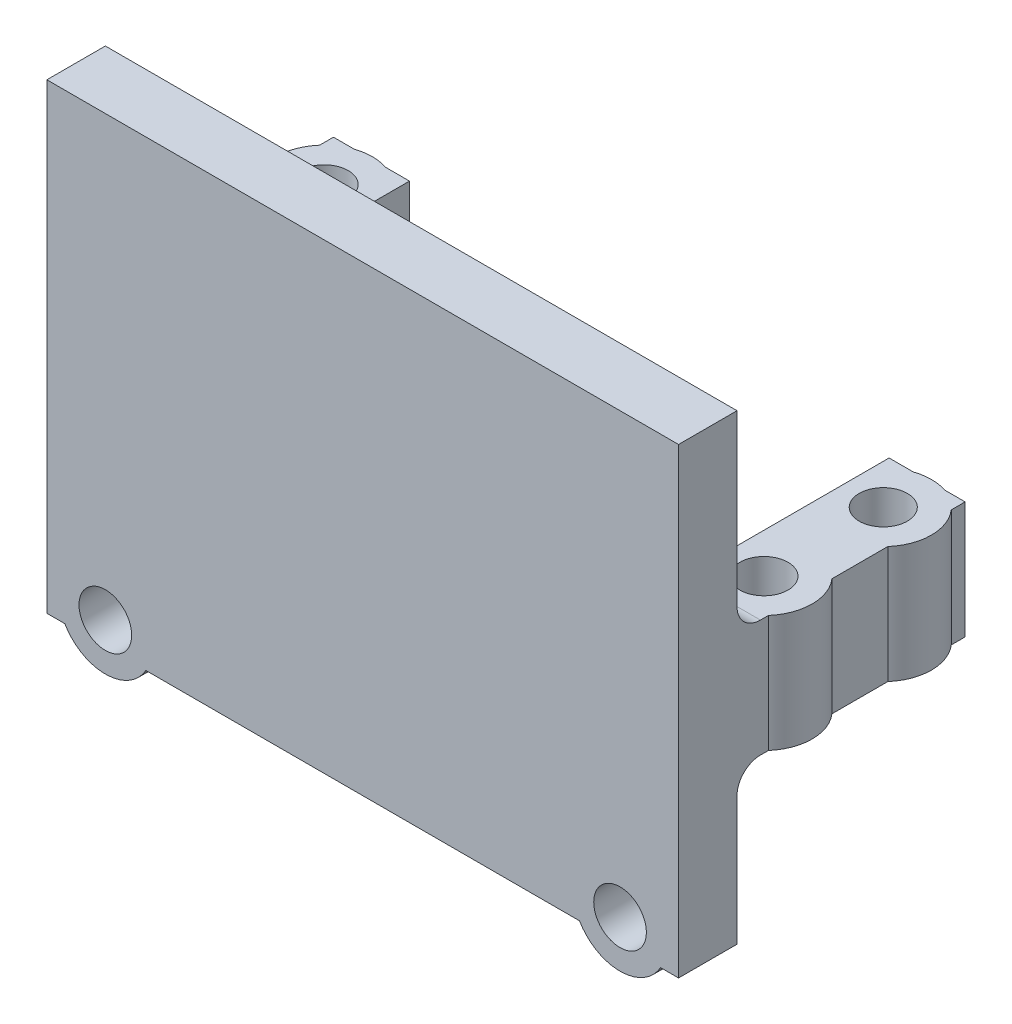
SolidWorks part; units mm, degrees
ref_plane "Front Plane" through (0, 0, 0) normal (0, 0, 1) x (1, 0, 0)
ref_plane "Top Plane" through (0, 0, 0) normal (0, 1, 0) x (1, 0, 0)
ref_plane "Right Plane" through (0, 0, 0) normal (1, 0, 0) x (0, 0, -1)
sketch "Sketch1" plane through (0, 0, 0) normal (0, 0, 1) x (1, 0, 0)
  line L1 (-27, 13.25) -> (27, 13.25)
  line L2 (-27, 13.25) -> (-27, -13.25)
  line L3 (-27, -13.25) -> (27, -13.25)
  line L4 (27, 13.25) -> (27, -13.25)
  dimension "D1" = 54
  dimension "D2" = 27
  dimension "D3" = 26.5
  dimension "D4" = 13.25
extrude "Boss-Extrude1" add sketch "Sketch1" along normal blind 5 contours L1 L4 L3 L2
sketch "Sketch2" plane through (0, 0, 0) normal (0, 0, -1) x (-1, 0, 0)
  line L0 (0, 0) -> (0, -16.6627) construction
  line L1 (-27, -13.25) -> (-20.5, -13.25)
  line L2 (-27, -13.25) -> (-27, -3.25)
  line L3 (-27, -3.25) -> (-20.5, -3.25)
  line L4 (-20.5, -13.25) -> (-20.5, -3.25)
  line L5 (20.5, -13.25) -> (20.5, -3.25)
  line L6 (27, -3.25) -> (20.5, -3.25)
  line L7 (27, -13.25) -> (27, -3.25)
  line L8 (27, -13.25) -> (20.5, -13.25)
  dimension "D1" = 6.5
  dimension "D2" = 10
extrude "Boss-Extrude2" add sketch "Sketch2" along normal blind 19.5
sketch "Sketch3" plane through (0, -13.25, 0) normal (0, -1, 0) x (1, 0, 0)
  line L0 (27, 5) -> (27, -19.5) construction
  line L1 (27, -19.5) -> (20.5, -19.5) construction
  line L2 (0, 0) -> (0, 8.5409) construction
  line L3 (-20.5, 0) -> (20.5, 0) construction
  circle A0 centre (23.9, -15.6) radius 2.06
  circle A1 centre (-23.9, -5.4) radius 2.06
  circle A2 centre (23.9, -5.4) radius 2.06
  circle A3 centre (-23.9, -15.6) radius 2.06
  dimension "D1" = 4.12
  dimension "D2" = 4.12
  dimension "D5" = 10.2
  dimension "D3" = 3.1
  dimension "D4" = 3.9
extrude "Cut-Extrude1" cut sketch "Sketch3" against normal blind 19
sketch "Sketch4" plane through (0, -13.25, 0) normal (0, -1, 0) x (1, 0, 0)
  line L0 (20.5, -19.5) -> (20.5, 0) construction
  line L1 (20.5, -17.9269) -> (20.5, -13.2731)
  line L2 (20.5, -7.7269) -> (20.5, -3.0731)
  line L3 (0, 0) -> (0, 16.8442) construction
  line L4 (-20.5, 0) -> (20.5, 0) construction
  line L5 (-20.5, -7.7269) -> (-20.5, -3.0731)
  line L6 (-20.5, -17.9269) -> (-20.5, -13.2731)
  circle A0 centre (23.9, -15.6) radius 2.06
  arc A1 (20.5, -17.9269) -> (20.5, -13.2731) centre (23.9, -15.6) ccw
  circle A2 centre (23.9, -5.4) radius 2.06
  arc A3 (20.5, -7.7269) -> (20.5, -3.0731) centre (23.9, -5.4) ccw
  arc A4 (-20.5, -7.7269) -> (-20.5, -3.0731) centre (-23.9, -5.4) cw
  circle A5 centre (-23.9, -5.4) radius 2.06
  arc A6 (-20.5, -17.9269) -> (-20.5, -13.2731) centre (-23.9, -15.6) cw
  circle A7 centre (-23.9, -15.6) radius 2.06
  dimension "D1" = 8.24
  dimension "D2" = 8.24
extrude "Boss-Extrude3" add sketch "Sketch4" against normal up to surface (10 mm away) up to face at (23.9, -3.25, -7.46)
fillet "Fillet1" radius 1 2 edges at (20.5, -8.25, 0) (-20.5, -8.25, 0)
fillet "Fillet2" radius 2 2 edges at (23.25, -3.25, 0) (-23.25, -3.25, 0)
sketch "Sketch5" plane through (0, -13.25, 0) normal (0, -1, 0) x (1, 0, 0)
  line L0 (-27, 5) -> (-27, 0)
  line L1 (27, 5) -> (-27, 5)
  line L2 (27, 5) -> (27, 0)
  line L5 (-27, 5) -> (-27, -2.6863) construction
  line L6 (-27, 0) -> (27, 0)
extrude "Boss-Extrude4" add sketch "Sketch5" along normal blind 13
sketch "Sketch6" plane through (0, 0, 0) normal (0, 0, -1) x (-1, 0, 0)
  line L1 (27, 13.25) -> (27, -1.25) construction
  line L2 (-27, -26.25) -> (-27, -13.25) construction
  line L3 (27, -26.25) -> (-27, -26.25) construction
  circle A0 centre (22, -24.25) radius 2.25
  circle A1 centre (-22, -24.25) radius 2.25
  dimension "D1" = 4.5
  dimension "D2" = 4.5
  dimension "D3" = 2
  dimension "D4" = 5
  dimension "D5" = 5
extrude "Cut-Extrude2" cut sketch "Sketch6" against normal blind 15
fillet "Fillet3" radius 2 1 edges at (23.25, -13.25, 0)
ref_plane "Plane1" through (0, 0, 0) normal (1, 0, 0) x (0, 0, -1)
sketch "Sketch7" plane through (0, 0, 0) normal (0, 0, -1) x (-1, 0, 0)
  circle A0 centre (22, -24.25) radius 2.25
  circle A1 centre (22, -24.25) radius 4
  circle A2 centre (-22, -24.25) radius 2.25
  circle A3 centre (-22, -24.25) radius 4
  dimension "D1" = 8
  dimension "D2" = 8
  dimension "D3" = 4.5
  dimension "D4" = 4.5
extrude "Boss-Extrude5" add sketch "Sketch7" against normal up to surface (5 mm away) up to face at (0, -15.3125, 5)
